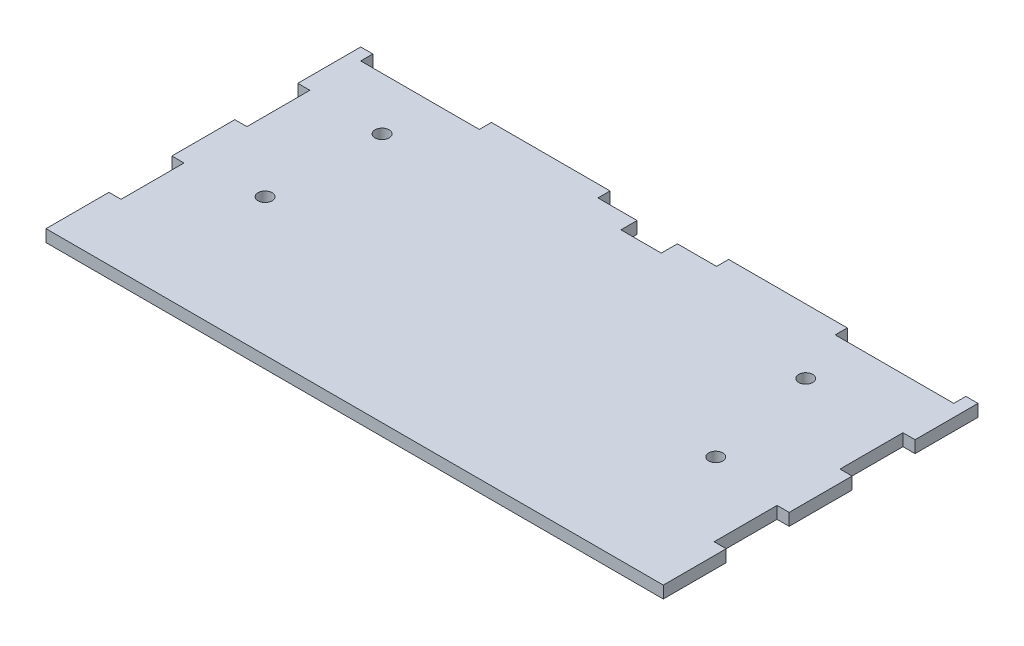
SolidWorks part; units mm, degrees
ref_plane "Front Plane" through (0, 0, 0) normal (0, 0, 1) x (1, 0, 0)
ref_plane "Top Plane" through (0, 0, 0) normal (0, 1, 0) x (1, 0, 0)
ref_plane "Right Plane" through (0, 0, 0) normal (1, 0, 0) x (0, 0, -1)
sketch "Sketch1" plane through (0, 0, 0) normal (0, 1, 0) x (1, 0, 0)
  line L6 (-73.5, 33) -> (-44.1, 33)
  line L12 (-73.5, 20.4) -> (-73.5, 4.8)
  line L14 (-76.5, 36) -> (-73.5, 36)
  line L16 (-76.5, 36) -> (-76.5, 20.4)
  line L20 (-76.5, 4.8) -> (-76.5, -10.8)
  line L23 (-76.5, -26.4) -> (-76.5, -42)
  line L24 (-76.5, -26.4) -> (-73.5, -26.4)
  line L25 (-76.5, -10.8) -> (-73.5, -10.8)
  line L26 (-76.5, 4.8) -> (-73.5, 4.8)
  line L27 (-76.5, 20.4) -> (-73.5, 20.4)
  line L29 (-73.5, 33) -> (-73.5, 36)
  line L30 (-73.5, -10.8) -> (-73.5, -26.4)
  line L31 (14.7, 36) -> (44.1, 36)
  line L32 (76.5, -26.4) -> (76.5, -42)
  line L33 (76.5, -26.4) -> (73.5, -26.4)
  line L34 (73.5, -10.8) -> (73.5, -26.4)
  line L35 (76.5, -10.8) -> (73.5, -10.8)
  line L36 (76.5, 4.8) -> (76.5, -10.8)
  line L37 (76.5, 4.8) -> (73.5, 4.8)
  line L38 (73.5, 20.4) -> (73.5, 4.8)
  line L39 (76.5, 20.4) -> (73.5, 20.4)
  line L40 (76.5, 36) -> (76.5, 20.4)
  line L41 (73.5, 33) -> (73.5, 36)
  line L43 (-14.7, 33) -> (-5, 33)
  line L44 (73.5, 36) -> (76.5, 36)
  line L45 (44.1, 33) -> (73.5, 33)
  line L46 (-44.1, 33) -> (-44.1, 36)
  line L47 (-14.7, 33) -> (-14.7, 36)
  line L48 (14.7, 33) -> (14.7, 36)
  line L49 (44.1, 33) -> (44.1, 36)
  line L50 (-44.1, 36) -> (-14.7, 36)
  line L62 (-76.5, -42) -> (76.5, -42)
  line L64 (0, 29) -> (-5, 29)
  line L65 (-5, 29) -> (-5, 32)
  line L66 (-5, 32) -> (-5, 33)
  line L67 (0, 29) -> (5, 29)
  line L68 (5, 29) -> (5, 33)
  line L69 (5, 33) -> (14.7, 33)
  circle A0 centre (-56.2, -8) radius 1.75
  circle A1 centre (-55.2, 20) radius 1.75
  circle A2 centre (49.8, 20) radius 1.75
  circle A3 centre (55.5, -8) radius 1.75
  point P0 (0, 0)
  point P4 (0, 0)
extrude "Boss-Extrude1" add sketch "Sketch1" along normal blind 3
